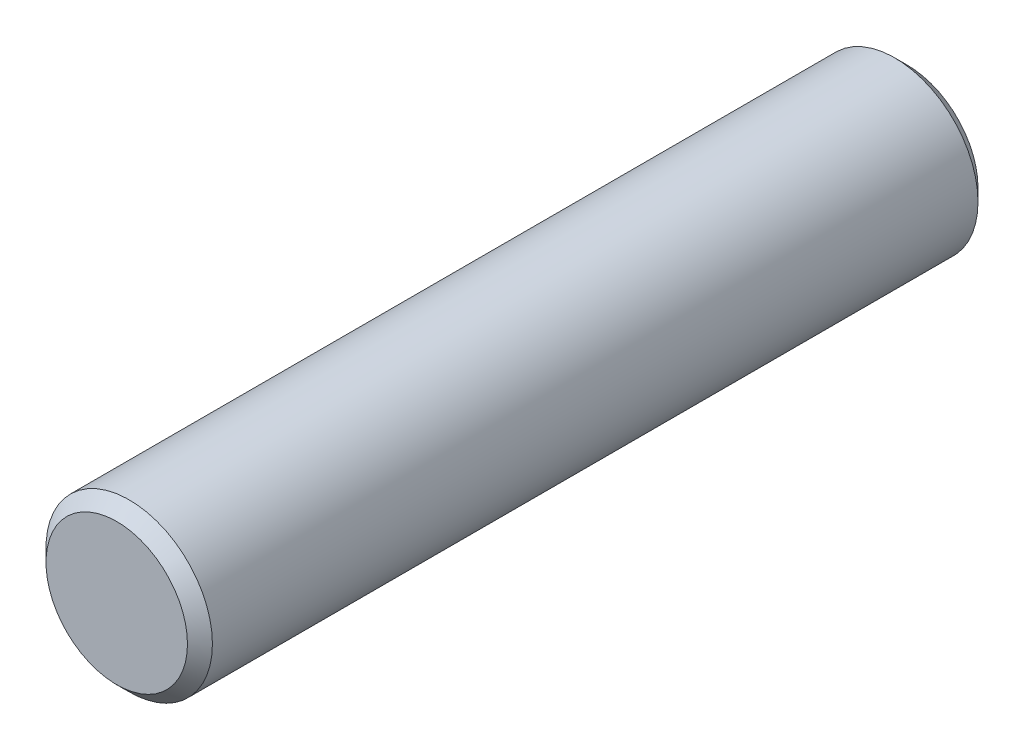
SolidWorks part; units mm, degrees
material "Plain Carbon Steel"
ref_plane "Front Plane" through (0, 0, 0) normal (0, 0, 1) x (1, 0, 0)
ref_plane "Top Plane" through (0, 0, 0) normal (0, 1, 0) x (1, 0, 0)
ref_plane "Right Plane" through (0, 0, 0) normal (1, 0, 0) x (0, 0, -1)
sketch "Sketch1" plane through (0, 0, 0) normal (0, 0, 1) x (1, 0, 0)
  circle A0 centre (0, 0) radius 4
  dimension "D1" = 8
extrude "Boss-Extrude1" add sketch "Sketch1" along normal blind 38
chamfer "Chamfer1" distance 0.6 angle 45 2 edges at (4, 0, 0) (4, 0, 38)
